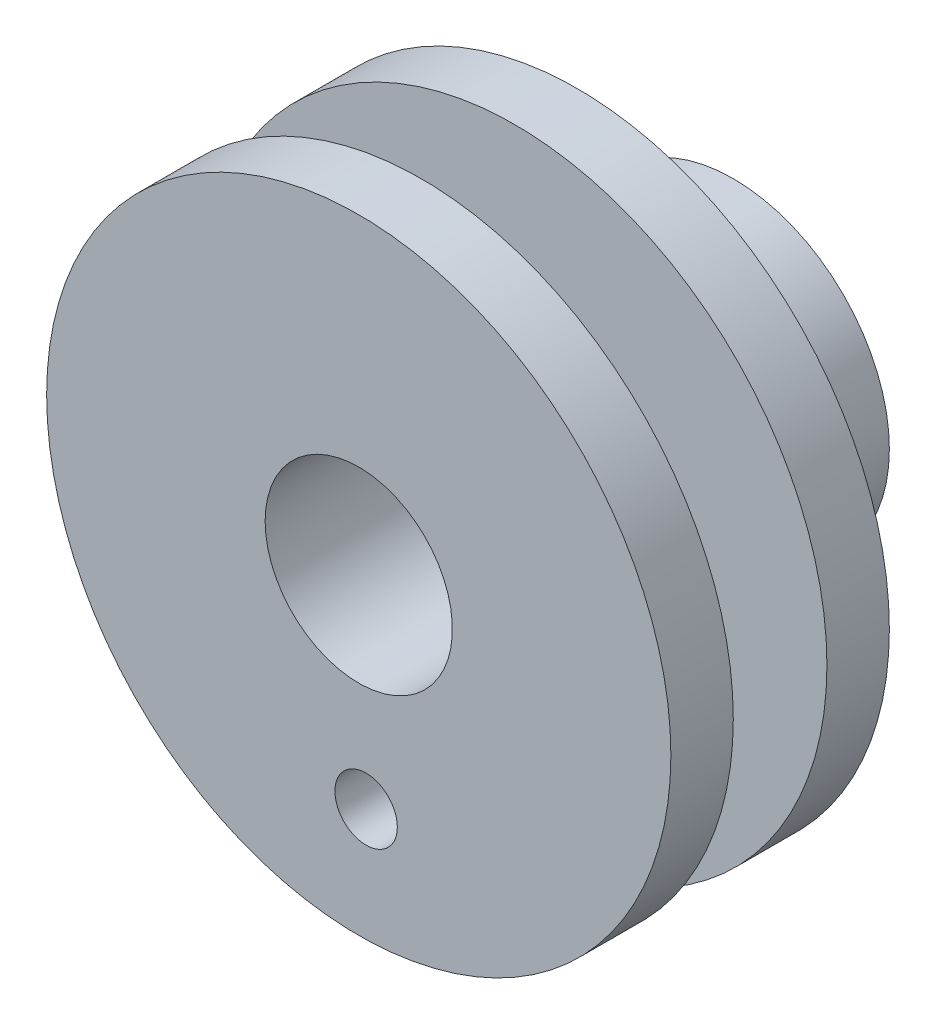
SolidWorks part; units mm, degrees
ref_plane "正面" through (0, 0, 0) normal (0, 0, 1) x (1, 0, 0)
ref_plane "平面" through (0, 0, 0) normal (0, 1, 0) x (1, 0, 0)
ref_plane "右側面" through (0, 0, 0) normal (1, 0, 0) x (0, 0, -1)
sketch "ｽｹｯﾁ1" plane through (0, 0, 0) normal (0, 0, 1) x (1, 0, 0)
  circle A0 centre (0, 0) radius 3
  circle A1 centre (0, 0) radius 5
  dimension "D1" = 6
  dimension "D2" = 10
extrude "ﾎﾞｽ - 押し出し1" add sketch "ｽｹｯﾁ1" along normal blind 5
sketch "ｽｹｯﾁ2" plane through (0, 0, 5) normal (0, 0, 1) x (1, 0, 0)
  circle A0 centre (0, 0) radius 3
  circle A1 centre (0, 0) radius 10
  dimension "D1" = 20
extrude "ﾎﾞｽ - 押し出し2" add sketch "ｽｹｯﾁ2" along normal blind 2
sketch "ｽｹｯﾁ3" plane through (0, 0, 7) normal (0, 0, 1) x (1, 0, 0)
  circle A0 centre (0, 0) radius 5
  dimension "D1" = 10
extrude "ﾎﾞｽ - 押し出し3" add sketch "ｽｹｯﾁ3" along normal blind 3
sketch "ｽｹｯﾁ4" plane through (0, 0, 10) normal (0, 0, 1) x (1, 0, 0)
  circle A0 centre (0, 0) radius 10
  dimension "D1" = 20
extrude "ﾎﾞｽ - 押し出し4" add sketch "ｽｹｯﾁ4" along normal blind 2
sketch "ｽｹｯﾁ5" plane through (0, 0, 7) normal (0, 0, -1) x (-1, 0, 0)
  circle A0 centre (0, 0) radius 3
extrude "ｶｯﾄ - 押し出し1" cut sketch "ｽｹｯﾁ5" against normal through all
hole_wizard "M3x0.5 ねじ穴1" positions "3Dｽｹｯﾁ1" profile "ｽｹｯﾁ6" tap size "M3x0.5" standard "JIS"
sketch3d "3Dｽｹｯﾁ1"
  point P0 (0.2512, -4.9937, 2.1439)
sketch "ｽｹｯﾁ6" plane through (0.2512, -4.9937, 2.1439) normal (0, 0, 1) x (0.9987, 0.0502, 0)
  line L0 (0, 0) -> (0, 2)
  line L1 (0, 2) -> (1.25, 2)
  line L2 (1.25, 2) -> (1.25, 0)
  line L5 (1.25, 0) -> (0, 0)
  line L11 (0, -6.35) -> (0, 107.95) construction
  dimension "次ｻｰﾌｪｽまでのねじ下穴ﾄﾞﾘﾙ直径" = 2.5
  dimension "次ｻｰﾌｪｽまでのねじ下穴ﾄﾞﾘﾙの深さ" = 2
cosmetic thread "穴のねじ山1" parameters "D2"=3
sketch "ｽｹｯﾁ7" plane through (0, 0, 12) normal (0, 0, 1) x (1, 0, 0)
  line L0 (0, 0) -> (0.2359, -6.3763)
  circle A0 centre (0.2359, -6.3763) radius 1
  dimension "D1" = 2
  dimension "D2" = 6.3763
extrude "ｶｯﾄ - 押し出し2" cut sketch "ｽｹｯﾁ7" against normal through all
